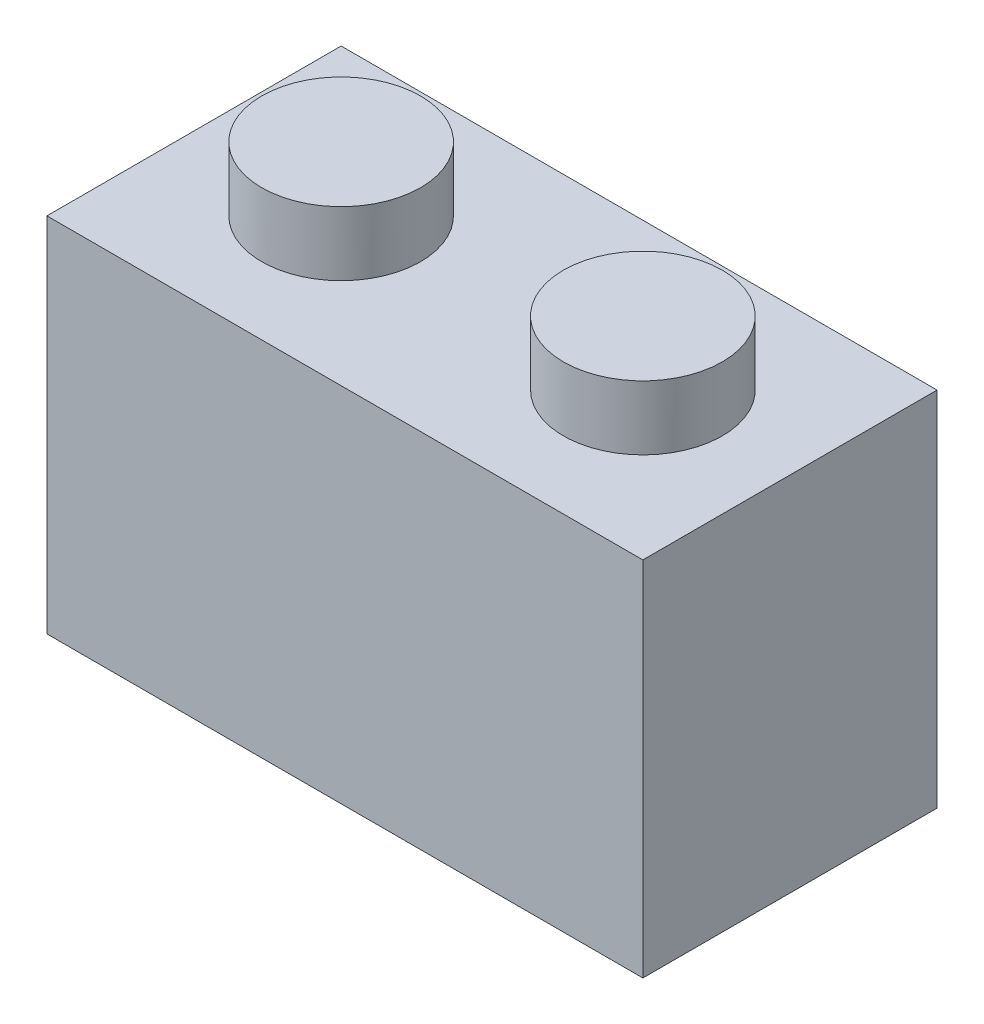
SolidWorks part; units mm, degrees
ref_plane "Спереди" through (0, 0, 0) normal (0, 0, 1) x (1, 0, 0)
ref_plane "Сверху" through (0, 0, 0) normal (0, 1, 0) x (1, 0, 0)
ref_plane "Справа" through (0, 0, 0) normal (1, 0, 0) x (0, 0, -1)
sketch "Эскиз1" plane through (0, 0, 0) normal (0, 1, 0) x (1, 0, 0)
  line L1 (0, 0) -> (15.8, 0)
  line L2 (0, 0) -> (0, 7.8)
  line L3 (0, 7.8) -> (15.8, 7.8)
  line L4 (15.8, 0) -> (15.8, 7.8)
  dimension "D1" = 15.8
  dimension "D2" = 7.8
extrude "Бобышка-Вытянуть2" add sketch "Эскиз1" along normal blind 9.6
sketch "Эскиз2" plane through (0, 9.6, 0) normal (0, 1, 0) x (1, 0, 0)
  line L0 (0, 7.8) -> (0, 0) construction
  line L1 (0, 0) -> (15.8, 0) construction
  circle A0 centre (3.9, 3.9) radius 2.1067
  circle A1 centre (11.9, 3.9) radius 2.1067
  dimension "D1" = 4.2133
  dimension "D2" = 3.9
  dimension "D3" = 3.9
  dimension "D4" = 2
extrude "Бобышка-Вытянуть3" add sketch "Эскиз2" along normal blind 1.7
sketch "Эскиз3" plane through (0, 0, 0) normal (0, -1, 0) x (1, 0, 0)
  line L0 (15.8, 0) -> (15.8, -7.8) construction
  line L1 (0, 0) -> (15.8, 0) construction
  circle A0 centre (11.9, -3.9) radius 2.5
  circle A1 centre (3.9, -3.9) radius 2.5
  dimension "D1" = 5
  dimension "D2" = 3.9
  dimension "D3" = 3.9
  dimension "D4" = 2
extrude "Вырез-Вытянуть1" cut sketch "Эскиз3" against normal blind 1.8
